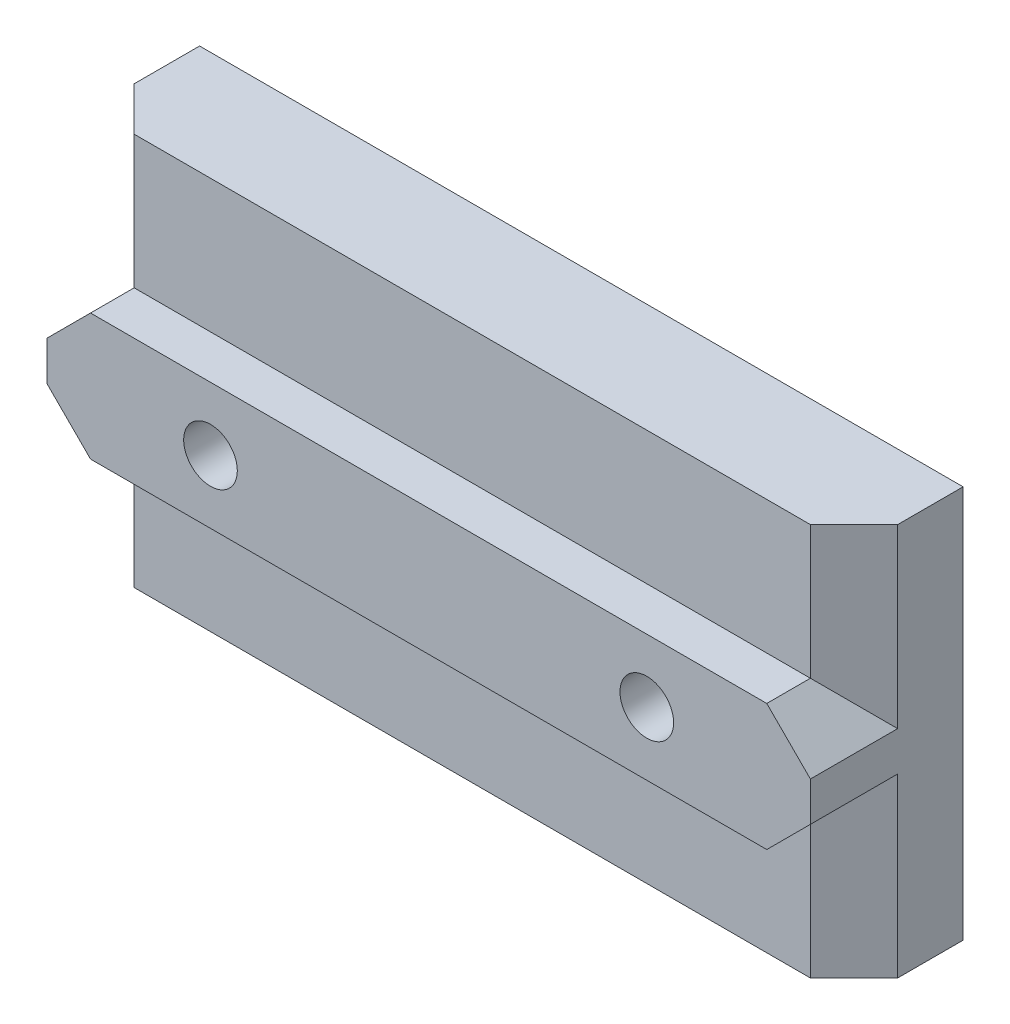
SolidWorks part; units mm, degrees
ref_plane "Front Plane" through (0, 0, 0) normal (0, 0, 1) x (1, 0, 0)
ref_plane "Top Plane" through (0, 0, 0) normal (0, 1, 0) x (1, 0, 0)
ref_plane "Right Plane" through (0, 0, 0) normal (1, 0, 0) x (0, 0, -1)
ref_plane "Plane1" through (0, 0, 8) normal (0, 0, 1) x (1, 0, 0)
sketch "Sketch1" plane through (0, 0, 8) normal (0, 0, 1) x (1, 0, 0)
  line L0 (17.5, -9) -> (17.5, 9)
  line L1 (17.5, 9) -> (-17.5, 9)
  line L2 (-17.5, 9) -> (-17.5, -9)
  line L3 (-17.5, -9) -> (17.5, -9)
extrude "Boss-Extrude1" add sketch "Sketch1" against normal blind 8
sketch "Sketch2" plane through (-17.5, 0, 0) normal (-1, 0, 0) x (0, 0, 1)
  line L0 (5, 2.9) -> (8, 2.9)
  line L1 (8, 2.9) -> (8, 9)
  line L2 (8, 9) -> (5, 9)
  line L3 (5, 9) -> (5, 2.9)
extrude "Cut-Extrude1" cut sketch "Sketch2" against normal through all
sketch "Sketch3" plane through (-17.5, 0, 0) normal (-1, 0, 0) x (0, 0, 1)
  line L0 (8, -2.9) -> (5, -2.9)
  line L1 (5, -2.9) -> (5, -9)
  line L2 (5, -9) -> (8, -9)
  line L3 (8, -9) -> (8, -2.9)
extrude "Cut-Extrude2" cut sketch "Sketch3" against normal through all
hole_wizard "M2 Clearance Hole1" positions "Sketch5" profile "Sketch4" hole size "M2" standard "ANSI Metric"
sketch "Sketch5" plane through (0, 0, 8) normal (0, 0, 1) x (1, 0, 0)
  point P0 (-10, 0)
  point P1 (10, 0)
sketch "Sketch4" plane through (-10, 0, 8) normal (1, 0, 0) x (0, -1, 0)
  line L0 (0, 0) -> (0, 8)
  line L1 (0, 8) -> (1.2295, 8)
  line L2 (1.2295, 8) -> (1.2295, 0)
  line L5 (1.2295, 0) -> (0, 0)
  line L11 (0, -6.35) -> (0, 107.95) construction
  dimension "Thru Hole Dia." = 2.459
  dimension "Thru Hole Depth" = 8
chamfer "Chamfer1" distance 0.2705 angle 45 4 edges at (11.2295, 0, 0) (11.2295, 0, 8) (-8.7705, 0, 0) (-8.7705, 0, 8)
chamfer "Chamfer2" distance 2 angle 45 8 edges at (-17.5, -5.95, 5) (-17.5, -2.9, 6.5) (17.5, -2.9, 6.5) (17.5, -5.95, 5) (-17.5, 5.95, 5) (-17.5, 2.9, 6.5) (17.5, 5.95, 5) (17.5, 2.9, 6.5)
sketch "Sketch6" plane through (0, 2.9, 0) normal (0, 1, 0) x (1, 0, 0)
  line L1 (-17.5, -7) -> (17.5, -7)
  line L2 (-17.5, -7) -> (-17.5, -8)
  line L3 (-17.5, -8) -> (17.5, -8)
  line L4 (17.5, -7) -> (17.5, -8)
  line L5 (-55, -8) -> (55, -8) construction
  line L7 (-17.5, -8) -> (-17.5, -3) construction
  line L8 (17.5, -3) -> (17.5, -8) construction
  dimension "D1" = 1
extrude "Cut-Extrude4" cut sketch "Sketch6" against normal blind 10 contours L3 L4 L1 L2
